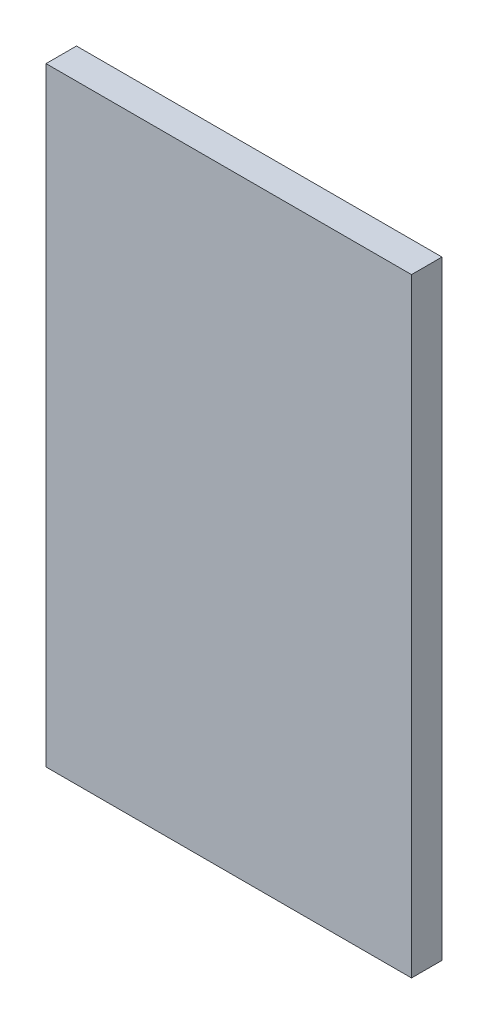
SolidWorks part; units mm, degrees
ref_plane "Front Plane" through (0, 0, 0) normal (0, 0, 1) x (1, 0, 0)
ref_plane "Top Plane" through (0, 0, 0) normal (0, 1, 0) x (1, 0, 0)
ref_plane "Right Plane" through (0, 0, 0) normal (1, 0, 0) x (0, 0, -1)
sketch "Sketch1" plane through (0, 0, 0) normal (0, 0, 1) x (1, 0, 0)
  line L1 (0, 0) -> (76.2, 0)
  line L2 (0, 0) -> (0, 127)
  line L3 (0, 127) -> (76.2, 127)
  line L4 (76.2, 0) -> (76.2, 127)
  dimension "D1" = 76.2
  dimension "D2" = 127
extrude "Boss-Extrude1" add sketch "Sketch1" along normal blind 6.35
